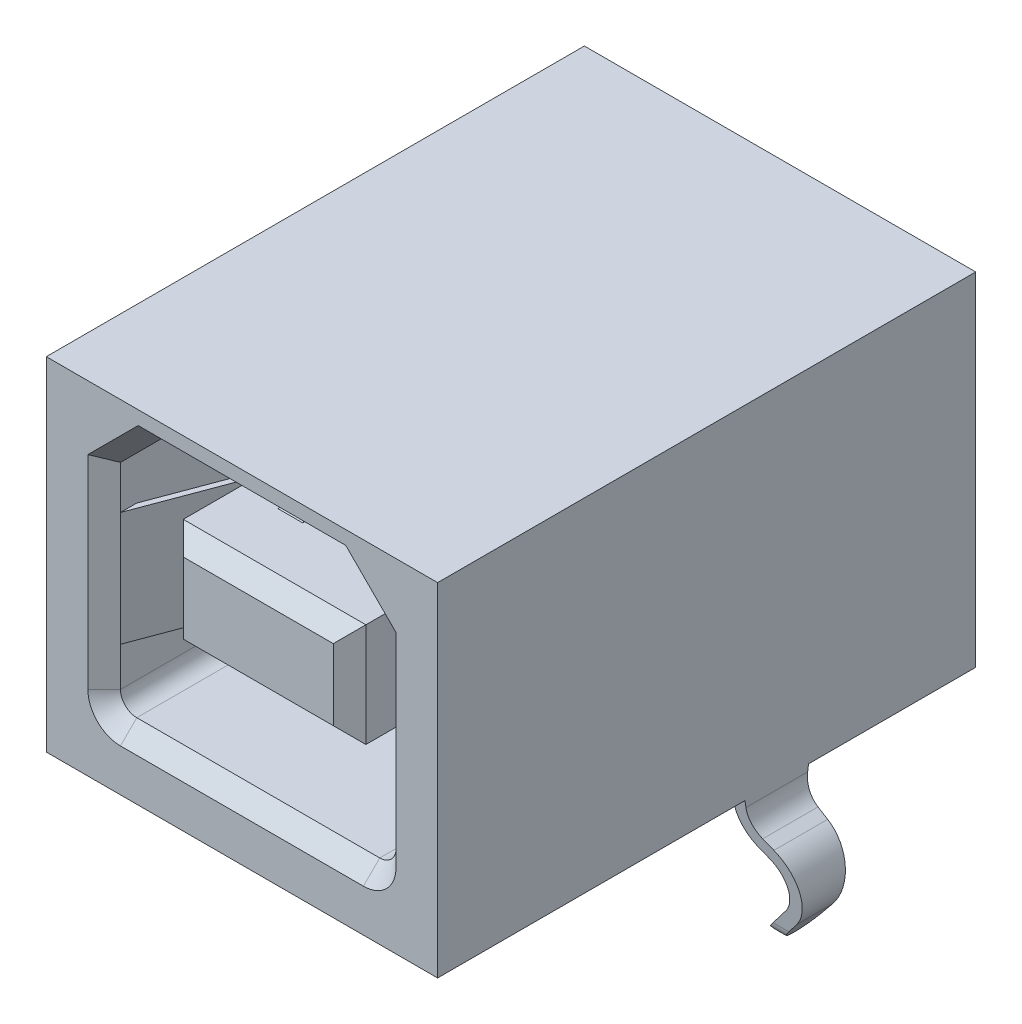
SolidWorks part; units mm, degrees
ref_plane "Front" through (0, 0, 0) normal (0, 0, 1) x (1, 0, 0)
ref_plane "Top" through (0, 0, 0) normal (0, 1, 0) x (1, 0, 0)
ref_plane "Right" through (0, 0, 0) normal (1, 0, 0) x (0, 0, -1)
sketch "Sketch1" plane through (0, 0, 0) normal (0, 0, 1) x (1, 0, 0)
  line L0 (-6, 5.25) -> (6, -5.25) construction
  line L1 (-6, 5.25) -> (6, 5.25)
  line L2 (-6, 5.25) -> (-6, -5.25)
  line L3 (-6, -5.25) -> (6, -5.25)
  line L4 (6, 5.25) -> (6, -5.25)
  dimension "D1" = 12
  dimension "D2" = 10.5
extrude "Base" add sketch "Sketch1" along normal mid plane 16.5
sketch "Sketch2" plane through (0, 0, 8.25) normal (0, 0, 1) x (1, 0, 0)
  line L0 (-2.975, 4.33) -> (-4.225, 3.08)
  line L1 (3.725, -3.45) -> (-3.725, -3.45)
  line L2 (4.225, -2.95) -> (4.225, 3.08)
  line L3 (2.975, 4.33) -> (-2.975, 4.33)
  line L4 (-4.225, -2.95) -> (-4.225, 3.08)
  line L5 (4.225, 3.08) -> (2.975, 4.33)
  line L6 (4.225, 4.33) -> (-4.225, -3.45) construction
  line L7 (6, 5.25) -> (-6, 5.25) construction
  line L9 (0, 0.44) -> (13.9883, 0.44) construction
  arc A0 (-3.725, -3.45) -> (-4.225, -2.95) centre (-3.725, -2.95) cw
  arc A1 (3.725, -3.45) -> (4.225, -2.95) centre (3.725, -2.95) ccw
  point P1 (4.225, 4.33)
  point P2 (-4.225, 4.33)
  point P12 (-4.225, -3.45)
  dimension "D1" = 0.5
  dimension "D2" = 4.81
  dimension "D3" = 8.45
  dimension "D5" = 7.78
extrude "Contact Opening" cut sketch "Sketch2" against normal blind 9
chamfer "Contact Opening Lead-in" distance 0.5 angle 45 8 edges at (-3.6, 3.705, 8.25) (0, 4.33, 8.25) (3.6, 3.705, 8.25) (4.225, 0.065, 8.25) (4.0786, -3.3036, 8.25) (0, -3.45, 8.25) (-4.0786, -3.3036, 8.25) (-4.225, 0.065, 8.25)
sketch "Sketch3" plane through (0, 0, -0.75) normal (0, 0, 1) x (1, 0, 0)
  line L0 (-2.8, 2.03) -> (2.8, -1.15) construction
  line L1 (-2.8, 2.03) -> (2.8, 2.03)
  line L2 (-2.8, 2.03) -> (-2.8, -1.15)
  line L3 (-2.8, -1.15) -> (2.8, -1.15)
  line L4 (2.8, 2.03) -> (2.8, -1.15)
  dimension "D1" = 5.6
  dimension "D2" = 3.18
extrude "Contact Area" add sketch "Sketch3" along normal blind 8.5
chamfer "Contact Area Lead-in" distance 0.5 angle 45 4 edges at (0, 2.03, 7.75) (2.8, 0.44, 7.75) (0, -1.15, 7.75) (-2.8, 0.44, 7.75)
ref_plane "Ground Leg Plane" through (0, 0, -2.15) normal (0, 0, 1) x (1, 0, 0)
sketch "Sketch4" plane through (0, 0, -2.15) normal (0, 0, 1) x (1, 0, 0)
  line L0 (0, 0) -> (0, -12.5407) construction
  line L1 (6.02, -5.058) -> (5.72, -5.1007)
  line L2 (6.4225, -5.35) -> (8.1, -5.35)
  line L3 (8.1, -5.35) -> (8.1, -5.65)
  line L5 (-6.1857, -5.65) -> (-8.1, -5.65)
  line L6 (-8.1, -5.35) -> (-8.1, -5.65)
  line L7 (-6.4225, -5.35) -> (-8.1, -5.35)
  line L8 (-6.02, -5.058) -> (-5.72, -5.1007)
  line L9 (6.1857, -5.65) -> (8.1, -5.65)
  arc A0 (6.02, -5.058) -> (6.4225, -5.35) centre (6.3271, -5.058) ccw
  arc A1 (-5.72, -5.1007) -> (-6.1857, -5.65) centre (-6.3271, -5.058) cw
  arc A2 (-6.02, -5.058) -> (-6.4225, -5.35) centre (-6.3271, -5.058) cw
  arc A5 (5.72, -5.1007) -> (6.1857, -5.65) centre (6.3271, -5.058) ccw
  dimension "D2" = 8.1
  dimension "D3" = 0.3
  dimension "D1" = 10.6
sketch "Sketch7" plane through (0, 0, 0) normal (0, 1, 0) x (1, 0, 0)
  line L0 (-4.225, -7.75) -> (-3.2152, -5.0513)
  line L1 (-3.3072, -2.7298) -> (-3.695, -1.9)
  line L2 (0, 0) -> (0, -8.8202) construction
  line L3 (-3.4657, -2.8039) -> (-3.8535, -1.9741)
  line L4 (-4.3889, -7.6887) -> (-3.3791, -4.99)
  line L5 (-3.695, -1.9) -> (-3.8535, -1.9741)
  line L6 (-4.225, -7.75) -> (-4.3889, -7.6887)
  line L7 (4.225, -7.75) -> (4.3889, -7.6887)
  line L8 (3.695, -1.9) -> (3.8535, -1.9741)
  line L9 (4.3889, -7.6887) -> (3.3791, -4.99)
  line L10 (3.4657, -2.8039) -> (3.8535, -1.9741)
  line L11 (3.3072, -2.7298) -> (3.695, -1.9)
  line L12 (4.225, -7.75) -> (3.2152, -5.0513)
  arc A0 (-3.2152, -5.0513) -> (-3.3072, -2.7298) centre (-6.025, -4) ccw
  arc A1 (-3.3791, -4.99) -> (-3.4657, -2.8039) centre (-6.025, -4) ccw
  arc A2 (3.3791, -4.99) -> (3.4657, -2.8039) centre (6.025, -4) cw
  arc A3 (3.2152, -5.0513) -> (3.3072, -2.7298) centre (6.025, -4) cw
  dimension "D2" = 3
  dimension "D5" = 3.75
  dimension "D1" = 5.85
  dimension "D3" = 1.8
  dimension "D4" = 0.53
  dimension "D6" = 0.175
extrude "Holding Tines" add sketch "Sketch7" along normal mid plane 3.5
ref_plane "Tail Plane" through (0, 0, -7.4) normal (0, 0, -1) x (-1, 0, 0)
ref_plane "Contact Plane" through (-1.25, 0, 0) normal (1, 0, 0) x (0, 0, -1)
ref_plane "SM TAILS PLANE" through (0.75, 0, 0) normal (1, 0, 0) x (0, 0, -1)
sketch "Sketch8" plane through (-1.25, 0, 0) normal (1, 0, 0) x (0, 0, -1)
  line L0 (0.75, 2.03) -> (-2.6953, 2.6783)
  line L1 (-4.4185, 2.4931) -> (-5.75, 1.93)
  line L2 (-7.25, 2.03) -> (0.75, 2.03) construction
  line L3 (0.75, 3.08) -> (0.75, -2.95) construction
  line L4 (-4.3503, 2.3319) -> (-5.6818, 1.7688)
  line L5 (0.7176, 1.858) -> (-2.7276, 2.5063)
  line L6 (0.7176, 1.858) -> (0.75, 2.03)
  line L7 (-5.6818, 1.7688) -> (-5.75, 1.93)
  line L8 (0.75, 2.03) -> (0.75, -1.15) construction
  line L9 (0.75, 0.44) -> (-6.7483, 0.44) construction
  line L10 (-5.6818, -0.8888) -> (-5.75, -1.05)
  line L11 (0.7176, -0.978) -> (0.75, -1.15)
  line L12 (0.7176, -0.978) -> (-2.7276, -1.6263)
  line L13 (-4.3503, -1.4519) -> (-5.6818, -0.8888)
  line L14 (-4.4185, -1.6131) -> (-5.75, -1.05)
  line L15 (0.75, -1.15) -> (-2.6953, -1.7983)
  arc A0 (-2.6953, 2.6783) -> (-4.4185, 2.4931) centre (-3.25, -0.27) ccw
  arc A1 (-2.7276, 2.5063) -> (-4.3503, 2.3319) centre (-3.25, -0.27) ccw
  arc A2 (-2.7276, -1.6263) -> (-4.3503, -1.4519) centre (-3.25, 1.15) cw
  arc A3 (-2.6953, -1.7983) -> (-4.4185, -1.6131) centre (-3.25, 1.15) cw
  dimension "D2" = 3
  dimension "D3" = 2.3
  dimension "D4" = 4
  dimension "D1" = 6.5
  dimension "D5" = 0.1
  dimension "D6" = 0.175
extrude "Contact" add sketch "Sketch8" along normal mid plane 0.75
pattern_linear "Contact Pattern" count 2 spacing 2.5 along (1, 0, 0) of "Contact"
sketch "Sketch12" plane through (0, -5.25, 0) normal (0, -1, 0) x (1, 0, 0)
  line L0 (0, 0) -> (0, 5.4435) construction
  line L1 (3.1821, 8.25) -> (4.725, 8.25) construction
  circle A0 centre (2.75, -0.75) radius 0.575
  circle A1 centre (-2.75, -0.75) radius 0.575
  point P5 (3.9536, 8.25)
  dimension "D1" = 1.15
  dimension "D2" = 2.75
  dimension "D3" = 9
sketch "Sketch13" plane through (0, 0, -2.15) normal (0, 0, 1) x (1, 0, 0)
  line L0 (6, -5.25) -> (6, -5.45)
  line L1 (6.4164, -6.1217) -> (6.736, -6.2805)
  line L2 (7.1575, -8.1791) -> (6.5272, -8.97)
  line L3 (6.8604, -7.9422) -> (6.23, -8.7332)
  line L4 (6.2473, -6.462) -> (6.567, -6.6208)
  line L5 (5.62, -5.25) -> (5.62, -5.45)
  line L6 (6.5272, -8.97) -> (6.23, -8.7332)
  line L7 (5.62, -5.25) -> (6, -5.25)
  line L8 (0, 0) -> (0, -9.739) construction
  line L9 (-6, -5.25) -> (6, -5.25) construction
  line L10 (6, -5.25) -> (6, 5.25) construction
  line L11 (-5.62, -5.25) -> (-6, -5.25)
  line L12 (-6.5272, -8.97) -> (-6.23, -8.7332)
  line L13 (-5.62, -5.25) -> (-5.62, -5.45)
  line L14 (-6.2473, -6.462) -> (-6.567, -6.6208)
  line L15 (-6.8604, -7.9422) -> (-6.23, -8.7332)
  line L16 (-7.1575, -8.1791) -> (-6.5272, -8.97)
  line L17 (-6.4164, -6.1217) -> (-6.736, -6.2805)
  line L18 (-6, -5.25) -> (-6, -5.45)
  arc A0 (6, -5.45) -> (6.4164, -6.1217) centre (6.75, -5.45) ccw
  arc A1 (6.736, -6.2805) -> (7.1575, -8.1791) centre (6.18, -7.4) cw
  arc A2 (6.567, -6.6208) -> (6.8604, -7.9422) centre (6.18, -7.4) cw
  arc A3 (5.62, -5.45) -> (6.2473, -6.462) centre (6.75, -5.45) ccw
  arc A4 (-5.62, -5.45) -> (-6.2473, -6.462) centre (-6.75, -5.45) cw
  arc A5 (-6.567, -6.6208) -> (-6.8604, -7.9422) centre (-6.18, -7.4) ccw
  arc A6 (-6.736, -6.2805) -> (-7.1575, -8.1791) centre (-6.18, -7.4) ccw
  arc A7 (-6, -5.45) -> (-6.4164, -6.1217) centre (-6.75, -5.45) cw
  dimension "D2" = 1.95
  dimension "D3" = 1.57
  dimension "D5" = 0.75
  dimension "D6" = 0.87
  dimension "D8" = 0.3472
  dimension "D1" = 0.2
  dimension "D4" = 0.38
  dimension "D7" = 0.18
extrude "TH Ground Legs" add sketch "Sketch13" along normal mid plane 1.95
sketch "Sketch14" plane through (0, 0, 0) normal (1, 0, 0) x (0, 0, -1)
  line L0 (3.125, -5.25) -> (3.125, -9)
  line L1 (2.6448, -8.5422) -> (3.125, -5.25)
  line L2 (3.125, -5.25) -> (8.25, -5.25) construction
  line L3 (1.6552, -8.5422) -> (1.175, -5.25)
  line L4 (1.175, -5.25) -> (1.175, -9)
  line L5 (3.125, -9) -> (1.175, -9)
  line L6 (2.15, -8.97) -> (2.15, -9.8721) construction
  line L7 (1.175, -8.97) -> (3.125, -8.97) construction
  arc A0 (1.6552, -8.5422) -> (2.6448, -8.5422) centre (2.15, -8.47) ccw
  point P1 (2.15, -9)
  dimension "D2" = 0.5
  dimension "D4" = 3.75
  dimension "D1" = 3.75
  dimension "D3" = 1.95
extrude "TH Ground Leg Shape" cut sketch "Sketch14" against normal through all and the other way through all
sketch "Sketch15" plane through (0, 0, -7.4) normal (0, 0, -1) x (-1, 0, 0)
  line L0 (-1.58, -5.25) -> (-0.92, -5.25)
  line L1 (-1.58, -5.25) -> (-1.58, -8.1)
  line L2 (-1.4588, -8.4) -> (-1.0412, -8.4)
  line L3 (-0.92, -5.25) -> (-0.92, -8.1)
  line L4 (-1.58, -8.1) -> (-1.4588, -8.4)
  line L5 (-0.92, -8.1) -> (-1.0412, -8.4)
  line L7 (0.92, -8.1) -> (1.0412, -8.4)
  line L8 (1.58, -8.1) -> (1.4588, -8.4)
  line L9 (0.92, -5.25) -> (0.92, -8.1)
  line L10 (1.4588, -8.4) -> (1.0412, -8.4)
  line L11 (1.58, -5.25) -> (1.58, -8.1)
  line L12 (1.58, -5.25) -> (0.92, -5.25)
  line L14 (0, 0) -> (0, -9.474) construction
  line L15 (6, -5.25) -> (-6, -5.25) construction
  dimension "D1" = 0.3
  dimension "D2" = 0.66
  dimension "D3" = 0.92
  dimension "D4" = 0.1212
  dimension "D5" = 3.15
  dimension "D6" = 0.1212
extrude "TH Tails" add sketch "Sketch15" along normal mid plane 0.25
pattern_linear "TH Tails Pattern" count 2 spacing 2 along (0, 0, 1) of "TH Tails"
